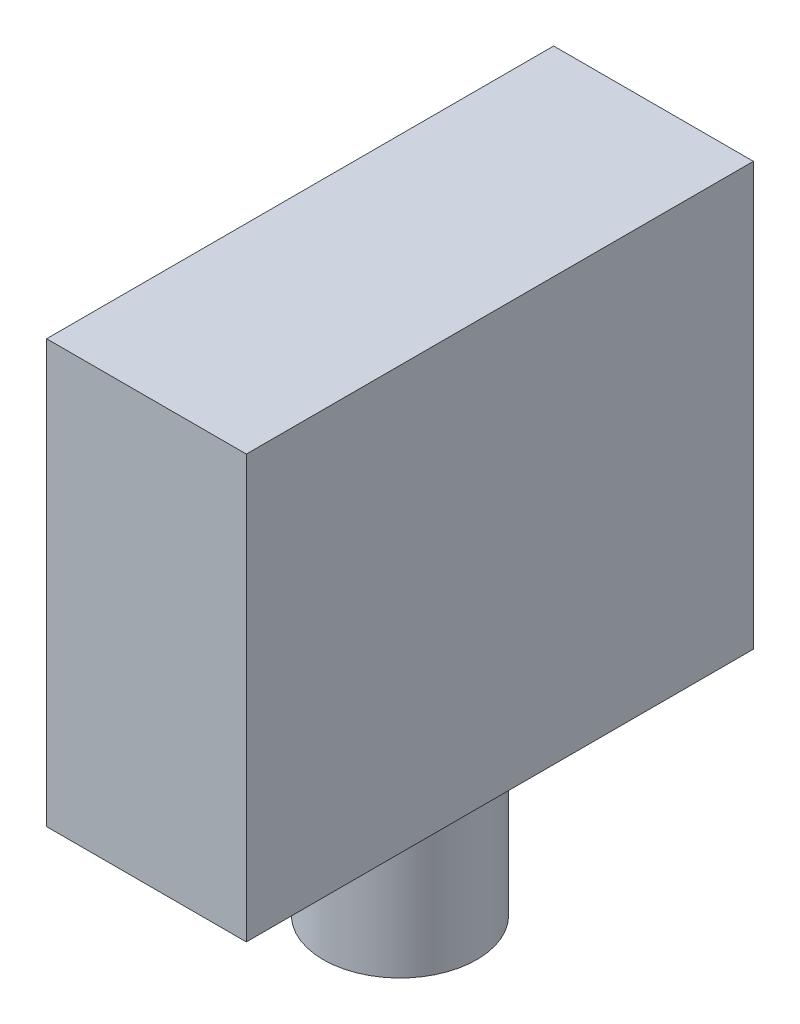
SolidWorks part; units mm, degrees
ref_plane "Ebene vorne" through (0, 0, 0) normal (0, 0, 1) x (1, 0, 0)
ref_plane "Ebene oben" through (0, 0, 0) normal (0, 1, 0) x (1, 0, 0)
ref_plane "Ebene rechts" through (0, 0, 0) normal (1, 0, 0) x (0, 0, -1)
sketch "Skizze1" plane through (0, 0, 0) normal (0, 1, 0) x (1, 0, 0)
  line L1 (-0.6029, 12.9412) -> (-13.6029, 12.9412)
  line L2 (-0.6029, 12.9412) -> (-0.6029, -20.0588)
  line L3 (-0.6029, -20.0588) -> (-13.6029, -20.0588)
  line L4 (-13.6029, 12.9412) -> (-13.6029, -20.0588)
  dimension "D1" = 13
  dimension "D2" = 33
extrude "Aufsatz-Linear austragen1" add sketch "Skizze1" along normal blind 27.5
sketch "Skizze2" plane through (0, 0, 0) normal (0, 1, 0) x (1, 0, 0)
  line L0 (-13.6029, 12.9412) -> (-0.6029, -20.0588) construction
  line L1 (-13.6029, -20.0588) -> (-0.6029, 12.9412) construction
  circle A0 centre (-7.1029, -3.5588) radius 5
  point P0 (-13.6029, 12.9412)
  point P1 (-0.6029, -20.0588)
  point P3 (-13.6029, -20.0588)
  point P5 (-0.6029, 12.9412)
  point P12 (-7.1029, -3.5588)
  dimension "D1" = 10
extrude "Aufsatz-Linear austragen2" add sketch "Skizze2" against normal blind 10
